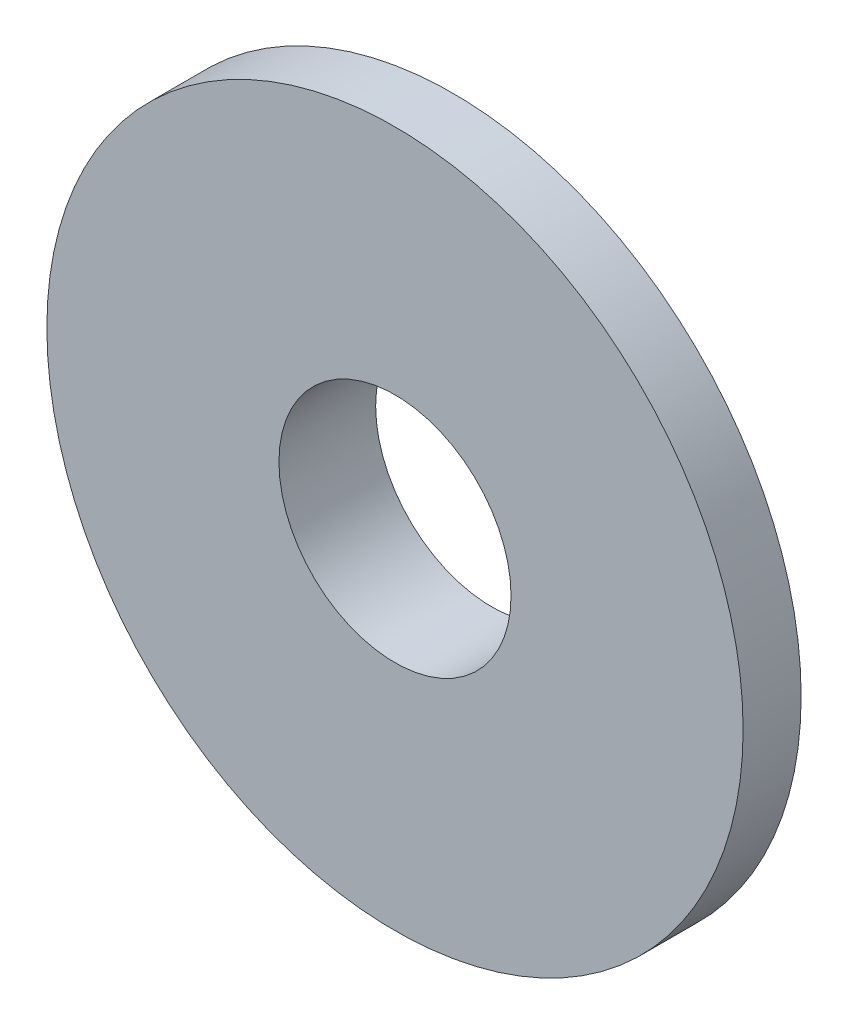
SolidWorks part; units mm, degrees
ref_plane "Front Plane" through (0, 0, 0) normal (0, 0, 1) x (1, 0, 0)
ref_plane "Top Plane" through (0, 0, 0) normal (0, 1, 0) x (1, 0, 0)
ref_plane "Right Plane" through (0, 0, 0) normal (1, 0, 0) x (0, 0, -1)
ref_plane "Plane1" through (0, 0, 0) normal (0, -1, 0) x (1, 0, 0)
sketch "Sketch1" plane through (0, 0, 0) normal (0, -1, 0) x (1, 0, 0)
  line L0 (5.5, 0) -> (9, 1)
  line L1 (9, 1) -> (9, 2.5)
  line L2 (9, 2.5) -> (3, 2.5)
  line L3 (3, 2.5) -> (3, 0)
  line L4 (3, 0) -> (5.5, 0)
  line L5 (0, 2.5) -> (0, 0) construction
  dimension "D1" = 3
  dimension "D2" = 5.5
  dimension "D3" = 9
  dimension "D4" = 1
  dimension "D5" = 2.5
revolve "Revolve1" add sketch "Sketch1" angle 360 about L5
